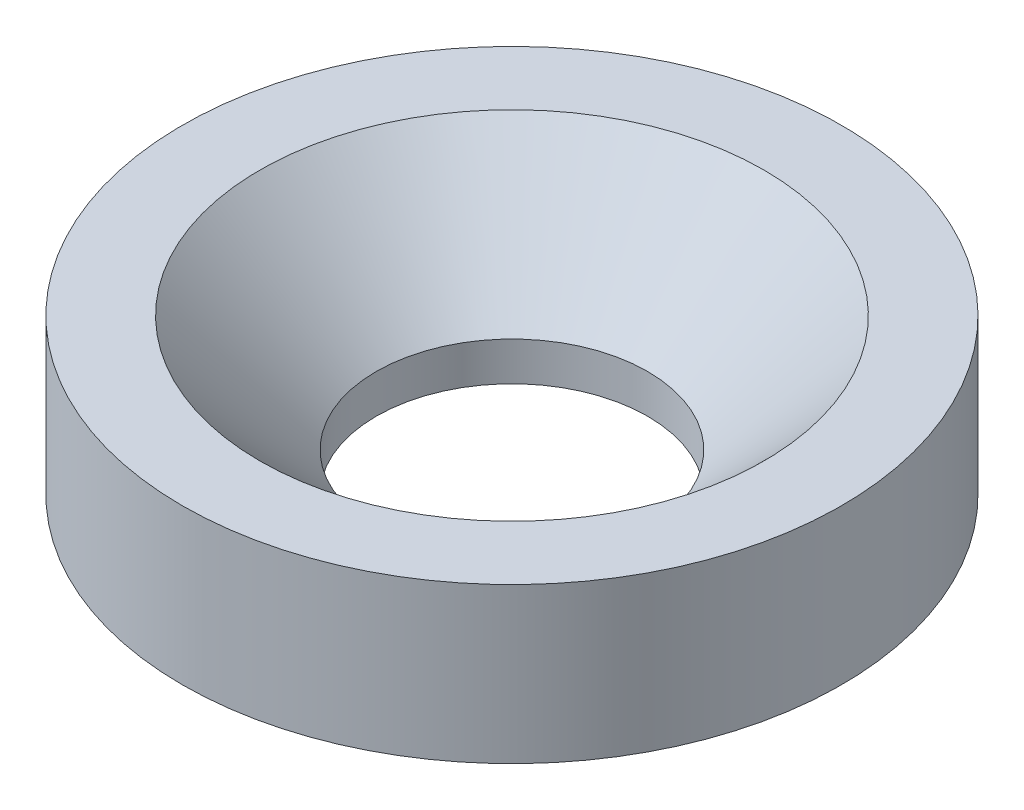
SolidWorks part; units mm, degrees
ref_plane "Front Plane" through (0, 0, 0) normal (0, 0, 1) x (1, 0, 0)
ref_plane "Top Plane" through (0, 0, 0) normal (0, 1, 0) x (1, 0, 0)
ref_plane "Right Plane" through (0, 0, 0) normal (1, 0, 0) x (0, 0, -1)
sketch "Sketch1" plane through (0, 0, 0) normal (0, 1, 0) x (1, 0, 0)
  circle A0 centre (0, 0) radius 1.75
  circle A1 centre (0, 0) radius 4.25
  point P2 (0, 0)
  dimension "D1" = 3.5
  dimension "D2" = 2.5
extrude "Boss-Extrude1" add sketch "Sketch1" along normal blind 2
chamfer "Chamfer1" distance 1.5 angle 45 1 edges at (0, 2, 1.75)
